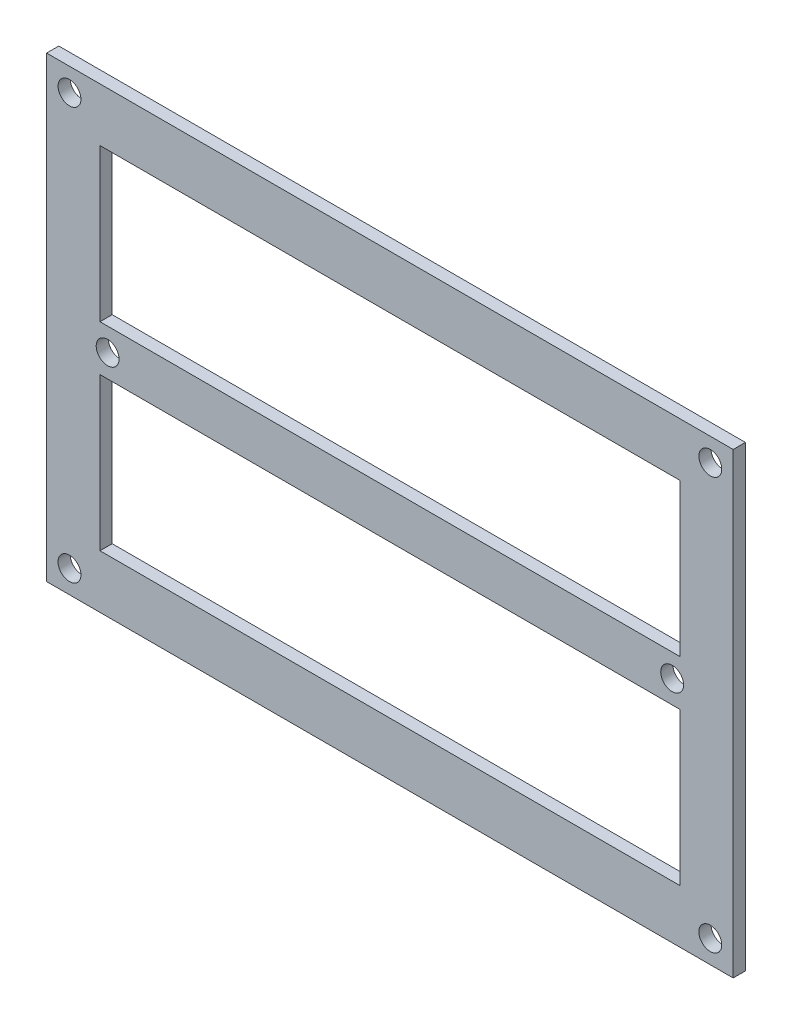
SolidWorks part; units mm, degrees
ref_plane "正面" through (0, 0, 0) normal (0, 0, 1) x (1, 0, 0)
ref_plane "平面" through (0, 0, 0) normal (0, 1, 0) x (1, 0, 0)
ref_plane "右側面" through (0, 0, 0) normal (1, 0, 0) x (0, 0, -1)
sketch "ｽｹｯﾁ2" plane through (0, 0, 0) normal (0, 0, 1) x (1, 0, 0)
  line L1 (-55.193, 27.3684) -> (34.807, 27.3684)
  line L2 (-55.193, 27.3684) -> (-55.193, -32.6316)
  line L3 (-55.193, -32.6316) -> (34.807, -32.6316)
  line L4 (34.807, 27.3684) -> (34.807, -32.6316)
  dimension "D1" = 90
  dimension "D2" = 60
extrude "ﾎﾞｽ - 押し出し1" add sketch "ｽｹｯﾁ2" along normal blind 1.6
sketch "ｽｹｯﾁ3" plane through (0, 0, 0) normal (0, 0, -1) x (-1, 0, 0)
  line L0 (-34.807, -32.6316) -> (-34.807, 27.3684) construction
  line L1 (-27.807, 20.3684) -> (48.193, 20.3684)
  line L2 (-27.807, 20.3684) -> (-27.807, 0.3684)
  line L3 (-27.807, 0.3684) -> (48.193, 0.3684)
  line L4 (48.193, 20.3684) -> (48.193, 0.3684)
  line L5 (55.193, 27.3684) -> (55.193, -32.6316) construction
  line L6 (-34.807, 27.3684) -> (55.193, 27.3684) construction
  line L7 (55.193, -32.6316) -> (-34.807, -32.6316) construction
  line L8 (-27.807, -5.6316) -> (48.193, -5.6316)
  line L9 (-27.807, -5.6316) -> (-27.807, -25.6316)
  line L10 (-27.807, -25.6316) -> (48.193, -25.6316)
  line L11 (48.193, -5.6316) -> (48.193, -25.6316)
  circle A0 centre (47.193, -2.6316) radius 1.5
  circle A1 centre (-26.807, -2.6316) radius 1.5
  circle A2 centre (52.193, 24.3684) radius 1.5
  circle A3 centre (-31.807, 24.3684) radius 1.5
  circle A4 centre (-31.807, -29.6316) radius 1.5
  circle A5 centre (52.193, -29.6316) radius 1.5
  dimension "D9" = 3
  dimension "D12" = 3
  dimension "D15" = 3
  dimension "D18" = 2
  dimension "D1" = 20
  dimension "D2" = 7
  dimension "D3" = 7
  dimension "D4" = 7
  dimension "D5" = 20
  dimension "D6" = 7
  dimension "D7" = 7
  dimension "D8" = 7
  dimension "D10" = 30
  dimension "D11" = 8
  dimension "D13" = 30
  dimension "D14" = 8
  dimension "D16" = 3
  dimension "D17" = 3
  dimension "D19" = 2
extrude "ｶｯﾄ - 押し出し1" cut sketch "ｽｹｯﾁ3" against normal through all
